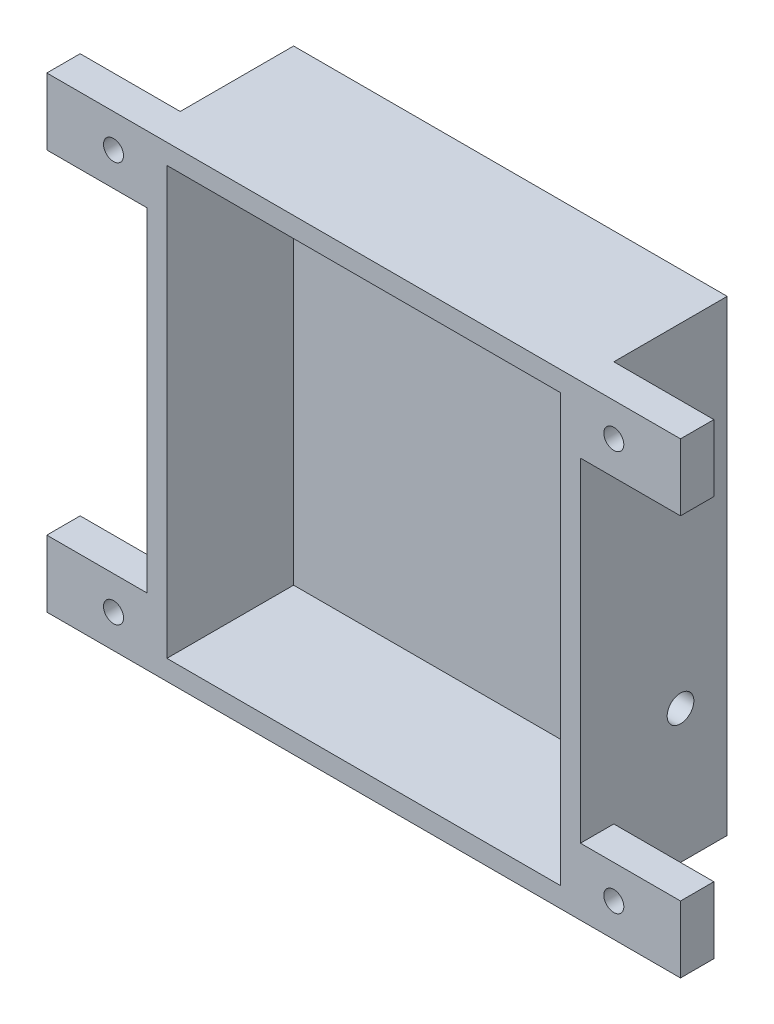
SolidWorks part; units mm, degrees
material "ABS"
ref_plane "Front Plane" through (0, 0, 0) normal (0, 0, 1) x (1, 0, 0)
ref_plane "Top Plane" through (0, 0, 0) normal (0, 1, 0) x (1, 0, 0)
ref_plane "Right Plane" through (0, 0, 0) normal (1, 0, 0) x (0, 0, -1)
sketch "Sketch1" plane through (0, 0, 0) normal (0, 0, 1) x (1, 0, 0)
  line L1 (0, 0) -> (59, 0)
  line L2 (0, 0) -> (0, 64)
  line L3 (0, 64) -> (59, 64)
  line L4 (59, 0) -> (59, 64)
  dimension "D1" = 64
  dimension "D2" = 59
extrude "Boss-Extrude1" add sketch "Sketch1" along normal blind 19
shell "Shell1" thickness 3
sketch "Sketch2" plane through (62, 0, 0) normal (1, 0, 0) x (0, 0, -1)
  line L3 (-19, -3) -> (-19, 67) construction
  circle A0 centre (-4, 17) radius 2
  dimension "D1" = 4
  dimension "D3" = 17
  dimension "D2" = 15
extrude "Cut-Extrude1" cut sketch "Sketch2" against normal blind 19
ref_plane "Plane1" through (0, 32, 0) normal (0, 1, 0) x (1, 0, 0)
sketch "Sketch3" plane through (62, 0, 0) normal (1, 0, 0) x (0, 0, -1)
  line L1 (-19, 67) -> (-14, 67)
  line L2 (-19, 67) -> (-19, 57)
  line L3 (-19, 57) -> (-14, 57)
  line L4 (-14, 67) -> (-14, 57)
  line L5 (-19, -3) -> (-14, -3)
  line L6 (-19, -3) -> (-19, 7)
  line L7 (-19, 7) -> (-14, 7)
  line L8 (-14, -3) -> (-14, 7)
  dimension "D1" = 5
  dimension "D2" = 10
  dimension "D3" = 10
  dimension "D4" = 5
extrude "Boss-Extrude2" add sketch "Sketch3" along normal blind 15
sketch "Sketch4" plane through (-3, 0, 0) normal (-1, 0, 0) x (0, 0, 1)
  line L1 (19, -3) -> (14, -3)
  line L2 (19, -3) -> (19, 7)
  line L3 (19, 7) -> (14, 7)
  line L4 (14, -3) -> (14, 7)
  line L5 (19, 67) -> (14, 67)
  line L6 (19, 67) -> (19, 57)
  line L7 (19, 57) -> (14, 57)
  line L8 (14, 67) -> (14, 57)
  dimension "D1" = 5
  dimension "D2" = 10
  dimension "D3" = 5
  dimension "D4" = 10
extrude "Boss-Extrude3" add sketch "Sketch4" along normal blind 15
sketch "Sketch5" plane through (0, 0, 14) normal (0, 0, -1) x (-1, 0, 0)
  line L1 (-77, 57) -> (-77, 67) construction
  line L3 (18, 7) -> (18, -3) construction
  line L4 (-62, 57) -> (-62, 67) construction
  line L5 (3, 67) -> (3, -3) construction
  circle A0 centre (-67, 62) radius 1.5
  circle A1 centre (8, 2) radius 1.5
  circle A2 centre (-67, 2) radius 1.5
  circle A3 centre (8, 62) radius 1.5
  point P8 (-77, 62)
  point P16 (18, 2)
  dimension "D1" = 3
  dimension "D2" = 3
  dimension "D3" = 3
  dimension "D4" = 3
  dimension "D5" = 5
  dimension "D6" = 5
extrude "Cut-Extrude2" cut sketch "Sketch5" against normal blind 10
